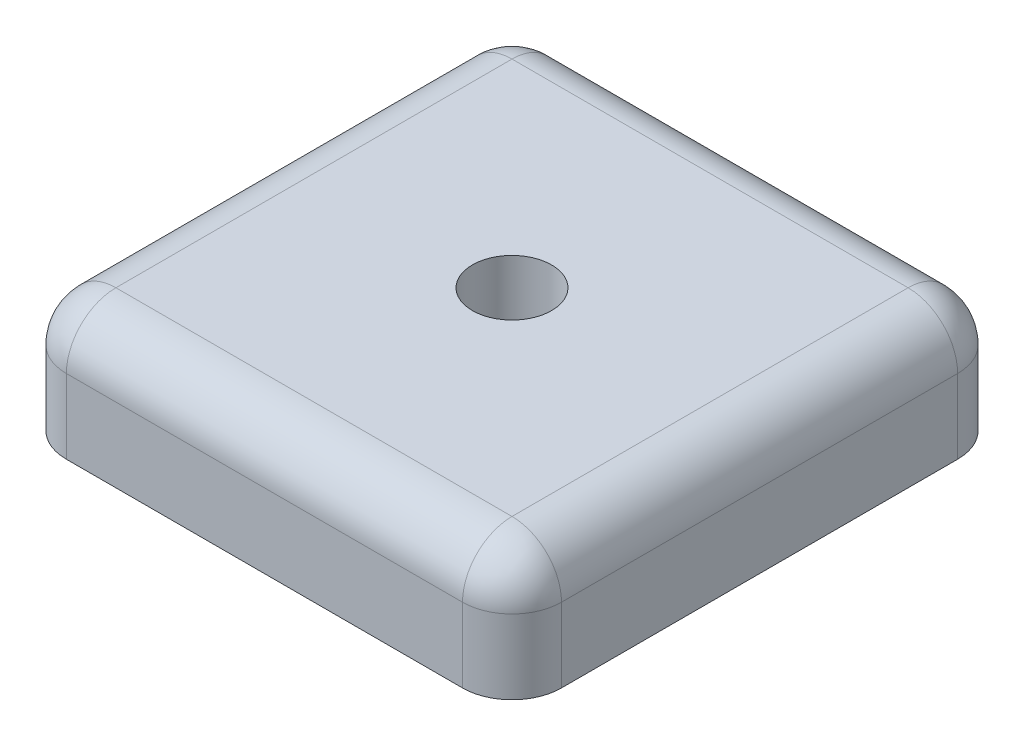
SolidWorks part; units mm, degrees
ref_plane "Front Plane" through (0, 0, 0) normal (0, 0, 1) x (1, 0, 0)
ref_plane "Top Plane" through (0, 0, 0) normal (0, 1, 0) x (1, 0, 0)
ref_plane "Right Plane" through (0, 0, 0) normal (1, 0, 0) x (0, 0, -1)
sketch "Sketch2" plane through (0, 0, 0) normal (0, 1, 0) x (1, 0, 0)
  line L0 (0, 20) -> (20, 20)
  line L1 (0, 0) -> (20, 0)
  line L2 (0, 0) -> (0, 20)
  line L4 (20, 0) -> (20, 20)
  dimension "D1" = 20
  dimension "D3" = 20
extrude "Boss-Extrude1" add sketch "Sketch2" along normal blind 5 contours L4 L0 L2 L1
sketch "Sketch3" plane through (0, 5, 0) normal (0, 1, 0) x (1, 0, 0)
  line L0 (0, 0) -> (20, 20) construction
  circle A0 centre (10, 10) radius 1.6
  dimension "D1" = 3.2
extrude "Cut-Extrude1" cut sketch "Sketch3" against normal through all
fillet "Fillet1" radius 2 8 edges at (0, 2.5, -20) (20, 2.5, -20) (20, 2.5, 0) (0, 2.5, 0) (10, 5, 0) (20, 5, -10) (10, 5, -20) (0, 5, -10)
